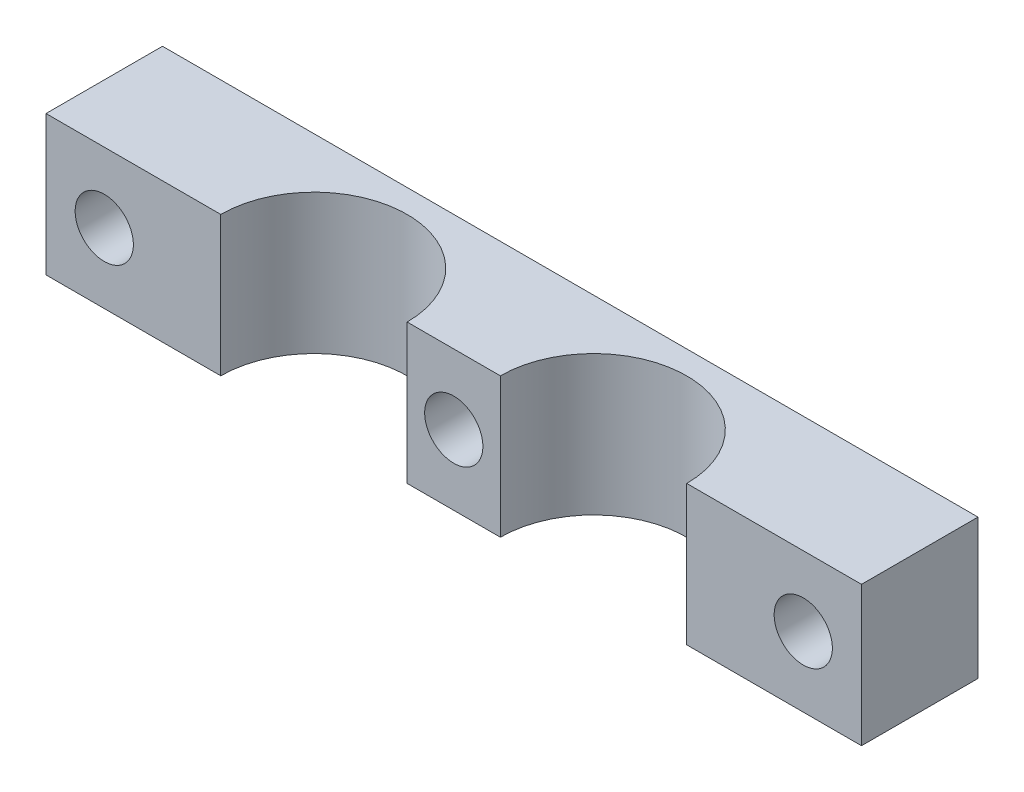
SolidWorks part; units mm, degrees
ref_plane "Front Plane" through (0, 0, 0) normal (0, 0, 1) x (1, 0, 0)
ref_plane "Top Plane" through (0, 0, 0) normal (0, 1, 0) x (1, 0, 0)
ref_plane "Right Plane" through (0, 0, 0) normal (1, 0, 0) x (0, 0, -1)
sketch "Sketch1" plane through (0, 0, 0) normal (0, 1, 0) x (1, 0, 0)
  line L1 (-35, 5) -> (35, 5)
  line L2 (-35, 5) -> (-35, -5)
  line L3 (-35, -5) -> (35, -5)
  line L4 (35, 5) -> (35, -5)
  line L5 (-35, 5) -> (35, -5) construction
  line L6 (-35, -5) -> (35, 5) construction
  circle A0 centre (0, 0) radius 2.5 construction
  circle A1 centre (-31.5, 0) radius 2.5 construction
  circle A2 centre (29.8554, 0) radius 2.5 construction
  circle A3 centre (-12, -5) radius 8
  circle A4 centre (12, -5) radius 8
  point P0 (0, 0)
  point P10 (-35, 0)
  point P15 (20, -5)
  dimension "D3" = 3.5
  dimension "D4" = 12
  dimension "D5" = 12
  dimension "D1" = 10
  dimension "D2" = 70
extrude "Boss-Extrude1" add sketch "Sketch1" along normal blind 12 contours A4 L3 L4 L1 L2 A3
sketch "Sketch2" plane through (0, 0, -5) normal (0, 0, -1) x (-1, 0, 0)
  line L0 (-35, 12) -> (-35, 0) construction
  line L1 (35, 12) -> (35, 0) construction
  line L3 (35, 0) -> (-35, 0) construction
  circle A0 centre (0, 6) radius 2.5
  circle A1 centre (-30, 6) radius 2.5
  circle A2 centre (30, 6) radius 2.5
  dimension "D2" = 5
  dimension "D4" = 5
  dimension "D5" = 5
  dimension "D1" = 6
  dimension "D3" = 5
  dimension "D6" = 5
  dimension "D7" = 35
  dimension "D8" = 6
  dimension "D11" = 30
  dimension "D12" = 35
extrude "Cut-Extrude1" cut sketch "Sketch2" against normal up to surface (10 mm away) up to face at (27.5, 6, 5)
